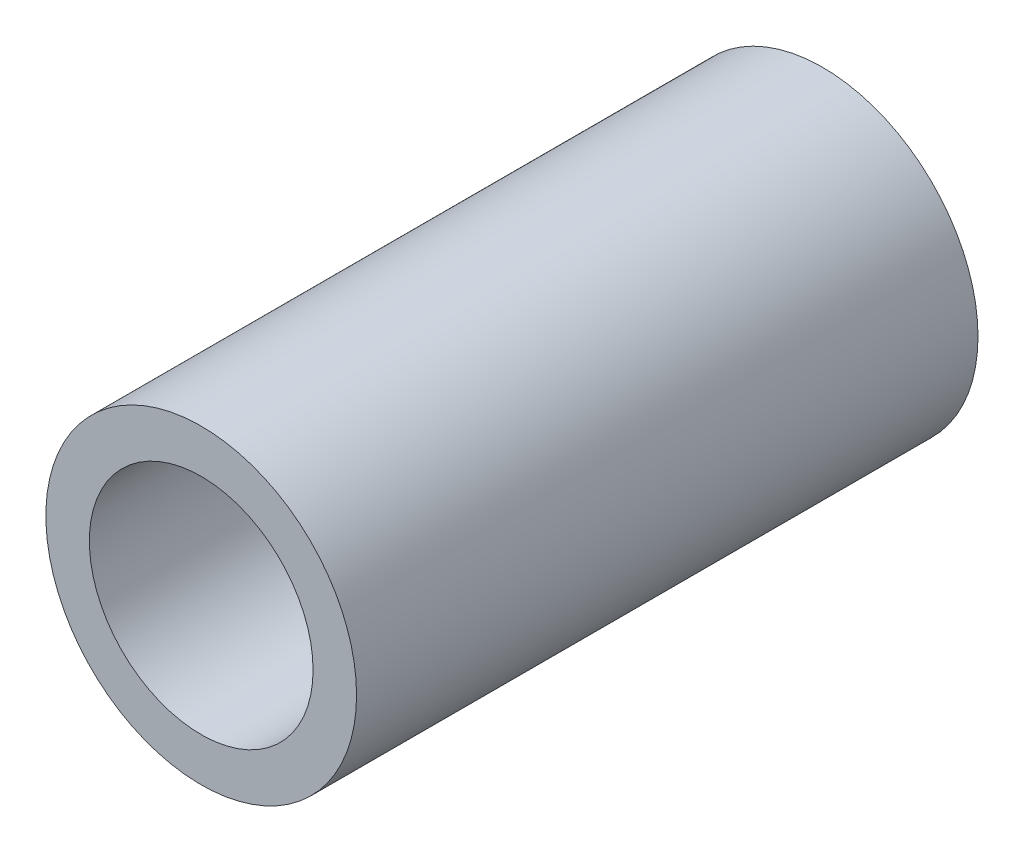
SolidWorks part; units mm, degrees
ref_plane "Front Plane" through (0, 0, 0) normal (0, 0, 1) x (1, 0, 0)
ref_plane "Top Plane" through (0, 0, 0) normal (0, 1, 0) x (1, 0, 0)
ref_plane "Right Plane" through (0, 0, 0) normal (1, 0, 0) x (0, 0, -1)
sketch "Sketch1" plane through (0, 0, 0) normal (0, 0, 1) x (1, 0, 0)
  circle A0 centre (0, 0) radius 1.5875
  circle A1 centre (0, 0) radius 1.143
  dimension "OD" = 3.175
  dimension "ID" = 2.286
extrude "Extrude1" add sketch "Sketch1" along normal mid plane 6.35
sketch "Sketch2" plane through (0, 0, 0) normal (1, 0, 0) x (0, 0, -1)
  line L0 (-3.175, -1.143) -> (3.175, -1.143) construction
  line L3 (3.175, 1.143) -> (-3.175, 1.143) construction
  line L5 (-3.175, -1.143) -> (3.175, -1.143)
  line L6 (3.175, 1.143) -> (-3.175, 1.143)
sketch "Sketch4" plane through (0, 0, 3.175) normal (0, 0, 1) x (1, 0, 0)
  line L0 (0, 0) -> (-0.8082, 0.8082)
  line L1 (0, -5.2388) -> (0, 5.2388) construction
  circle A0 centre (0, 0) radius 1.143 construction
  dimension "D1" = 45
